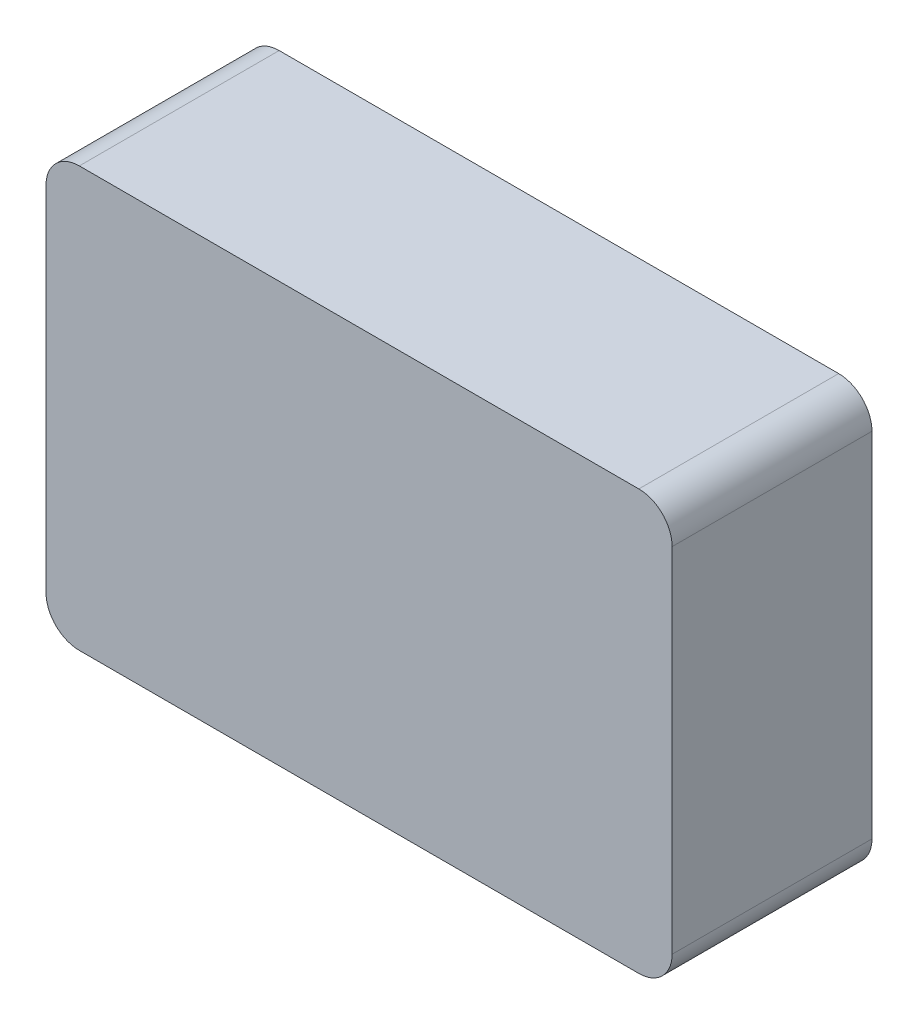
SolidWorks part; units mm, degrees
ref_plane "Front Plane" through (0, 0, 0) normal (0, 0, 1) x (1, 0, 0)
ref_plane "Top Plane" through (0, 0, 0) normal (0, 1, 0) x (1, 0, 0)
ref_plane "Right Plane" through (0, 0, 0) normal (1, 0, 0) x (0, 0, -1)
sketch "Sketch1" plane through (0, 0, 0) normal (0, 0, 1) x (1, 0, 0)
  line L1 (-42, 31.5) -> (42, 31.5)
  line L2 (-47, 26.5) -> (-47, -26.5)
  line L3 (-42, -31.5) -> (42, -31.5)
  line L4 (47, 26.5) -> (47, -26.5)
  arc A0 (42, -31.5) -> (47, -26.5) centre (42, -26.5) ccw
  arc A1 (47, 26.5) -> (42, 31.5) centre (42, 26.5) ccw
  arc A2 (-42, -31.5) -> (-47, -26.5) centre (-42, -26.5) cw
  arc A3 (-47, 26.5) -> (-42, 31.5) centre (-42, 26.5) cw
  point P9 (47, 31.5)
  point P14 (-47, 31.5)
  dimension "D5" = 5
  dimension "D1" = 94
  dimension "D2" = 47
  dimension "D3" = 63
  dimension "D4" = 31.5
extrude "Boss-Extrude1" add sketch "Sketch1" along normal blind 30
sketch "Sketch2" plane through (0, -31.5, 0) normal (0, -1, 0) x (1, 0, 0)
  line L0 (-35, 10) -> (-27, 10) construction
  line L1 (-35, 12) -> (-27, 12)
  line L2 (-35, 8) -> (-27, 8)
  line L3 (-19, 10) -> (-11, 10) construction
  line L4 (-19, 12) -> (-11, 12)
  line L5 (-19, 8) -> (-11, 8)
  line L6 (-3, 10) -> (5, 10) construction
  line L7 (-3, 12) -> (5, 12)
  line L8 (-3, 8) -> (5, 8)
  line L9 (-42, 0) -> (42, 0) construction
  line L10 (-47, 30) -> (-47, 0) construction
  arc A0 (-35, 12) -> (-35, 8) centre (-35, 10) ccw
  arc A1 (-27, 8) -> (-27, 12) centre (-27, 10) ccw
  arc A2 (-19, 12) -> (-19, 8) centre (-19, 10) ccw
  arc A3 (-11, 8) -> (-11, 12) centre (-11, 10) ccw
  arc A4 (-3, 12) -> (-3, 8) centre (-3, 10) ccw
  arc A5 (5, 8) -> (5, 12) centre (5, 10) ccw
  circle A6 centre (15, 10) radius 2
  point P2 (-31, 10)
  point P9 (-15, 10)
  point P14 (1, 10)
  point P27 (0, 0)
  point P28 (0, 0)
  point P29 (0, 0)
  dimension "D11" = 4
  dimension "D1" = 8
  dimension "D2" = 4
  dimension "D3" = 12
  dimension "D4" = 8
  dimension "D5" = 8
  dimension "D6" = 4
  dimension "D7" = 8
  dimension "D8" = 8
  dimension "D9" = 8
  dimension "D10" = 4
  dimension "D12" = 10
extrude "Cut-Extrude1" cut sketch "Sketch2" against normal blind 2
sketch "Sketch3" plane through (-47, 0, 0) normal (-1, 0, 0) x (0, 0, 1)
  line L0 (30, 26.5) -> (0, 26.5) construction
  line L1 (5, 26.5) -> (25, 26.5)
  line L2 (5, 26.5) -> (5, -26.5)
  line L3 (5, -26.5) -> (25, -26.5)
  line L4 (25, 26.5) -> (25, -26.5)
  line L5 (30, -26.5) -> (0, -26.5) construction
  line L6 (30, 26.5) -> (30, -26.5) construction
  line L7 (0, 26.5) -> (0, -26.5) construction
  dimension "D1" = 5
  dimension "D2" = 5
extrude "Cut-Extrude2" cut sketch "Sketch3" against normal blind 5
